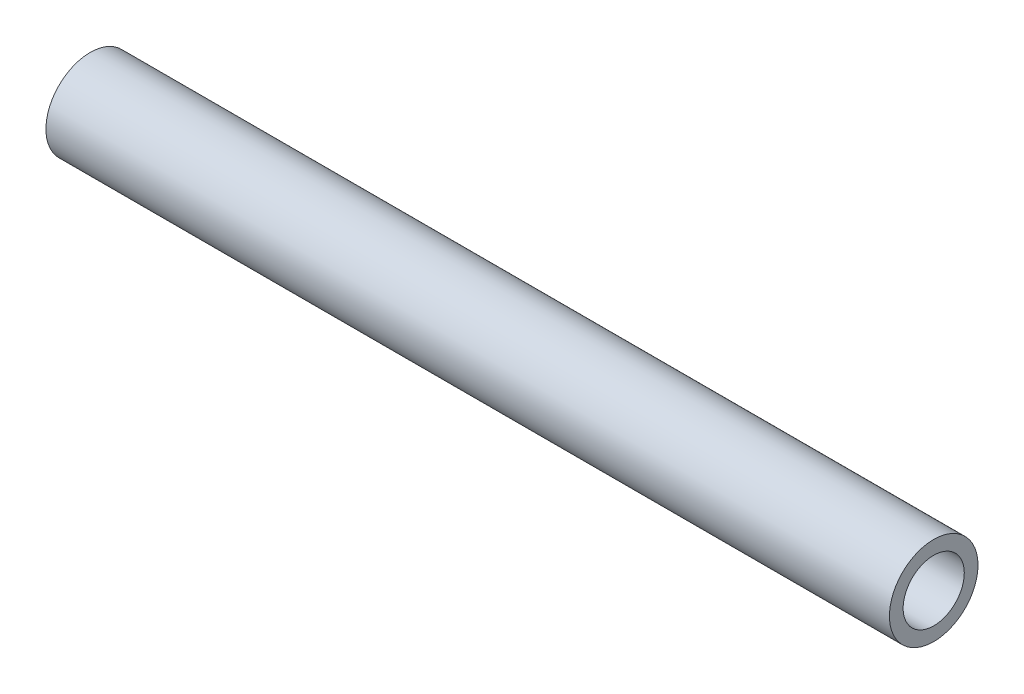
SolidWorks part; units mm, degrees
material "PVC 0.007 Plasticized"
ref_plane "Front Plane" through (0, 0, 0) normal (0, 0, 1) x (1, 0, 0)
ref_plane "Top Plane" through (0, 0, 0) normal (0, 1, 0) x (1, 0, 0)
ref_plane "Right Plane" through (0, 0, 0) normal (1, 0, 0) x (0, 0, -1)
sketch "Sketch1" plane through (0, 0, 0) normal (1, 0, 0) x (0, 0, -1)
  circle A0 centre (0, 0) radius 10.668
  circle A1 centre (0, 0) radius 7.366
  dimension "D1" = 21.336
  dimension "D2" = 14.732
extrude "Boss-Extrude1" add sketch "Sketch1" against normal blind 203.2
